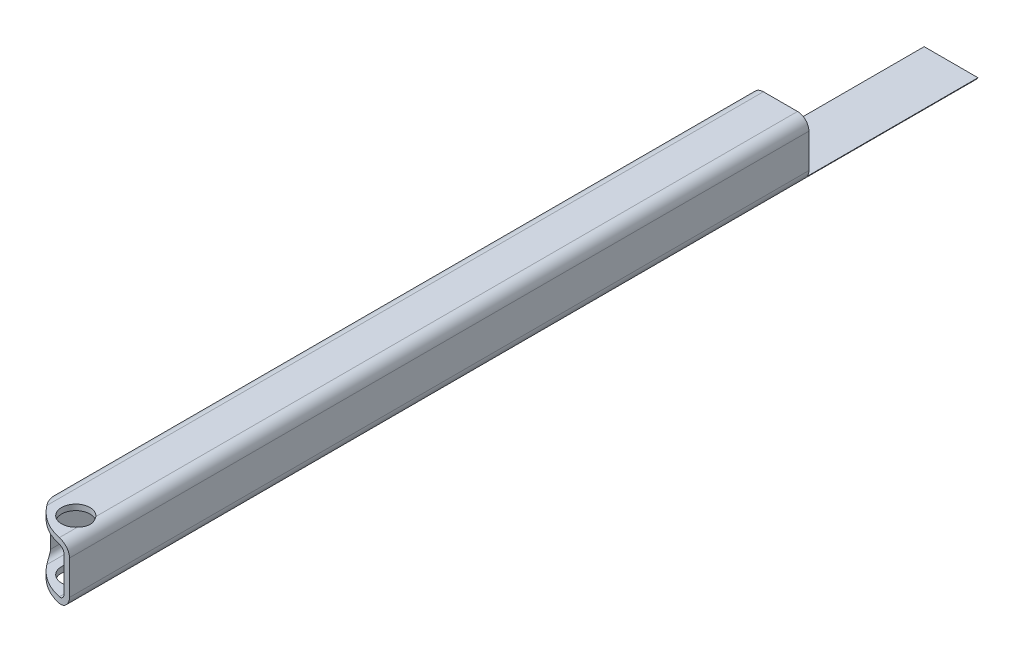
SolidWorks part; units mm, degrees
ref_plane "Front Plane" through (0, 0, 0) normal (0, 0, 1) x (1, 0, 0)
ref_plane "Top Plane" through (0, 0, 0) normal (0, 1, 0) x (1, 0, 0)
ref_plane "Right Plane" through (0, 0, 0) normal (1, 0, 0) x (0, 0, -1)
sketch "Sketch1" plane through (0, 0, 0) normal (0, 0, 1) x (1, 0, 0)
  line L0 (2.54, 1.27) -> (10.16, 1.27)
  line L1 (2.54, 0) -> (10.16, 0)
  line L2 (0, 2.54) -> (0, 10.16)
  line L3 (2.54, 12.7) -> (10.16, 12.7)
  line L4 (12.7, 2.54) -> (12.7, 10.16)
  line L5 (11.43, 2.54) -> (11.43, 10.16)
  line L6 (2.54, 11.43) -> (10.16, 11.43)
  line L7 (1.27, 2.54) -> (1.27, 10.16)
  arc A0 (2.54, 0) -> (0, 2.54) centre (2.54, 2.54) cw
  arc A1 (10.16, 0) -> (12.7, 2.54) centre (10.16, 2.54) ccw
  arc A2 (10.16, 12.7) -> (12.7, 10.16) centre (10.16, 10.16) cw
  arc A3 (0, 10.16) -> (2.54, 12.7) centre (2.54, 10.16) cw
  arc A4 (10.16, 1.27) -> (11.43, 2.54) centre (10.16, 2.54) ccw
  arc A5 (10.16, 11.43) -> (11.43, 10.16) centre (10.16, 10.16) cw
  arc A6 (1.27, 10.16) -> (2.54, 11.43) centre (2.54, 10.16) cw
  arc A7 (2.54, 1.27) -> (1.27, 2.54) centre (2.54, 2.54) cw
  point P7 (0, 0)
  point P10 (12.7, 0)
  point P15 (0, 12.7)
  dimension "D3" = 2.54
  dimension "D1" = 12.7
  dimension "D2" = 12.7
  dimension "D4" = 1.27
extrude "Boss-Extrude1" add sketch "Sketch1" along normal blind 203.2
sketch "Sketch2" plane through (0, 12.7, 0) normal (0, 1, 0) x (1, 0, 0)
  line L1 (12.7, -203.2) -> (12.7, 0) construction
  line L2 (10.16, -203.2) -> (2.54, -203.2) construction
  circle A0 centre (7.747, -196.85) radius 3.175
  dimension "D1" = 6.35
  dimension "D2" = 4.953
  dimension "D3" = 6.35
extrude "Cut-Extrude1" cut sketch "Sketch2" against normal through all
sketch "Sketch3" plane through (0, 0, 0) normal (-1, 0, 0) x (0, 0, 1)
  line L1 (0, 12.7) -> (38.1, 12.7)
  line L2 (0, 12.7) -> (0, 1.27)
  line L3 (0, 1.27) -> (38.1, 1.27)
  line L4 (38.1, 12.7) -> (38.1, 1.27)
  dimension "D1" = 38.1
  dimension "D2" = 0
extrude "Cut-Extrude2" cut sketch "Sketch3" against normal through all
sketch "Sketch4" plane through (0, 12.7, 0) normal (0, 1, 0) x (1, 0, 0)
  line L1 (0, -203.2) -> (12.7, -203.2)
  line L2 (0, -203.2) -> (0, -190.5)
  line L5 (0, -203.2) -> (0, -38.1) construction
  arc A0 (0, -190.5) -> (12.7, -203.2) centre (12.7, -190.5) ccw
  point P1 (0, 0)
  point P4 (0, 0)
  point P5 (0, -190.5)
  point P10 (0, 0)
  point P11 (0, 0)
  dimension "D2" = 25.4
extrude "Cut-Extrude3" cut sketch "Sketch4" against normal through all
